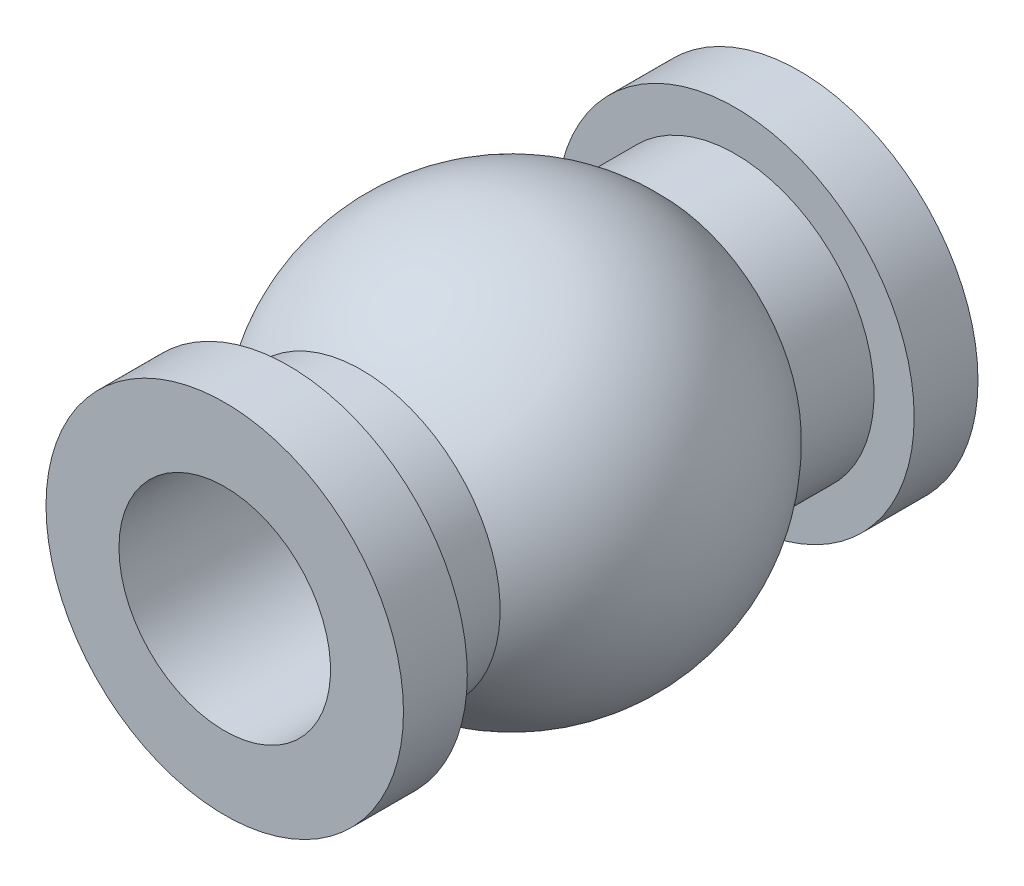
SolidWorks part; units mm, degrees
ref_plane "Front Plane" through (0, 0, 0) normal (0, 0, 1) x (1, 0, 0)
ref_plane "Top Plane" through (0, 0, 0) normal (0, 1, 0) x (1, 0, 0)
ref_plane "Right Plane" through (0, 0, 0) normal (1, 0, 0) x (0, 0, -1)
sketch "Sketch1" plane through (0, 0, 0) normal (0, 1, 0) x (1, 0, 0)
  line L0 (1.4732, 4.0005) -> (1.4732, -4.0005)
  line L1 (1.4732, -4.0005) -> (2.4892, -4.0005)
  line L2 (2.4892, -4.0005) -> (2.4892, -3.1115)
  line L3 (2.4892, -3.1115) -> (1.9304, -3.1115)
  line L4 (1.9304, -3.1115) -> (1.9304, -2.0955)
  line L5 (1.4732, 4.0005) -> (2.4892, 4.0005)
  line L6 (2.4892, 4.0005) -> (2.4892, 3.1115)
  line L7 (1.9304, 2.0955) -> (1.9304, 3.1115)
  line L8 (1.9304, 3.1115) -> (2.4892, 3.1115)
  line L9 (0, 2.773) -> (0, -2.9056) construction
  arc A0 (1.9304, -2.0955) -> (1.9304, 2.0955) centre (0, 0) ccw
  point P13 (1.4732, 0)
  dimension "D4" = 1.016
  dimension "D7" = 2.8491
  dimension "D1" = 1.016
  dimension "D2" = 0.889
  dimension "D3" = 8.001
  dimension "D5" = 1.9304
  dimension "D6" = 1.4732
revolve "Revolve1" add sketch "Sketch1" angle 360 about L9
